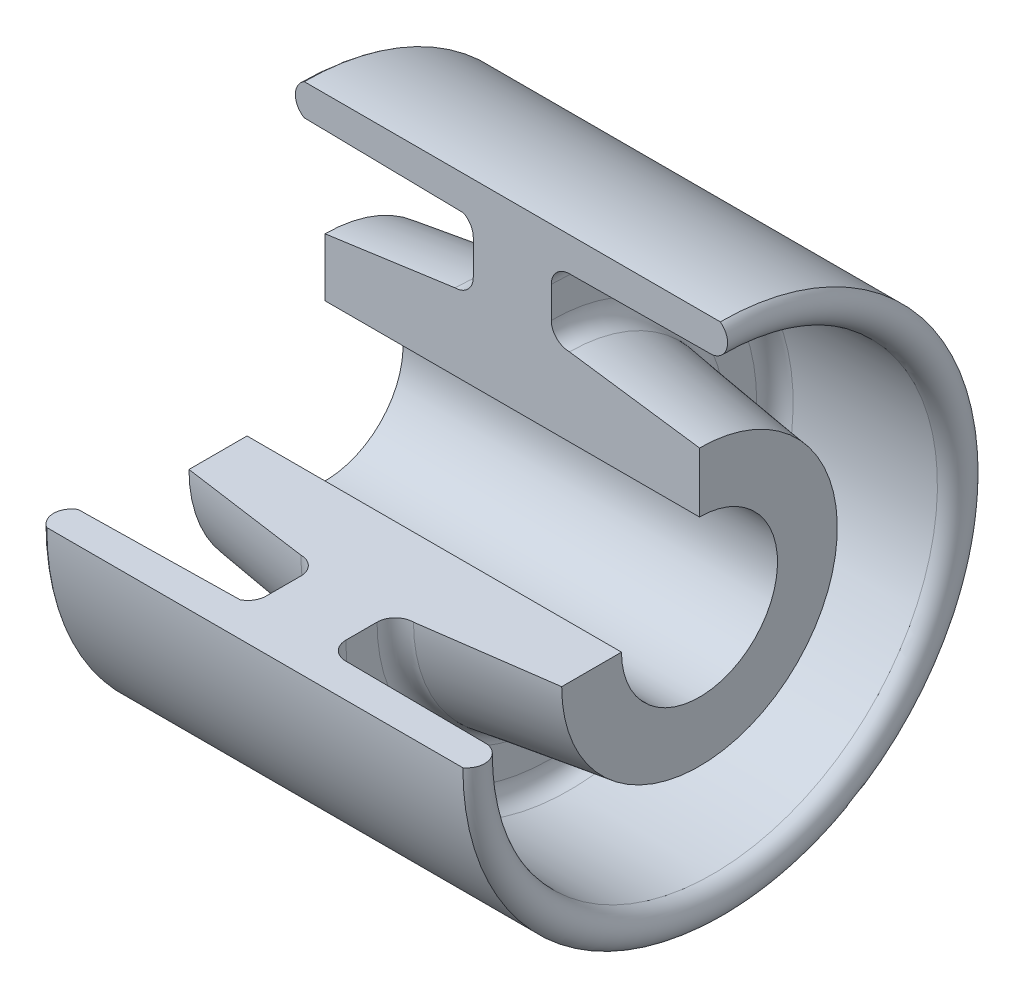
SolidWorks part; units mm, degrees
ref_plane "Front Plane" through (0, 0, 0) normal (0, 0, 1) x (1, 0, 0)
ref_plane "Top Plane" through (0, 0, 0) normal (0, 1, 0) x (1, 0, 0)
ref_plane "Right Plane" through (0, 0, 0) normal (1, 0, 0) x (0, 0, -1)
sketch "Sketch1" plane through (0, 0, 0) normal (0, 0, 1) x (1, 0, 0)
  line L0 (-50.6321, 30.5282) -> (29.3679, 30.5282)
  line L1 (25.3679, -3.9718) -> (25.3679, -18.9718) construction
  line L2 (35.3913, -18.9718) -> (-59.7616, -18.9718) construction
  line L4 (-18.1321, 20.8659) -> (-18.1321, 14.1905)
  line L5 (-3.1321, 20.5282) -> (-3.1321, 14.5282)
  line L7 (-46.6321, -3.9718) -> (25.3679, -3.9718)
  line L10 (25.3679, -3.9718) -> (25.3679, 7.5282)
  line L11 (-46.6321, -3.9718) -> (-46.6321, 7.1905)
  line L14 (-50.6321, 24.506) -> (-20.0232, 23.9742)
  line L15 (27.8679, 24.2766) -> (0.3679, 24.0282)
  line L16 (-46.6321, 7.1905) -> (-21.6321, 10.6905)
  line L18 (25.3679, 7.5282) -> (0.3679, 11.0282)
  arc A0 (27.8679, 24.2766) -> (29.3679, 30.5282) centre (27.2716, 27.7254) ccw
  arc A1 (-50.6321, 30.5282) -> (-50.6321, 24.506) centre (-48.848, 27.5171) ccw
  arc A2 (0.3679, 24.0282) -> (-3.1321, 20.5282) centre (0.3679, 20.5282) ccw
  arc A4 (-3.1321, 14.5282) -> (0.3679, 11.0282) centre (0.3679, 14.5282) ccw
  arc A5 (-21.6321, 10.6905) -> (-18.1321, 14.1905) centre (-21.6321, 14.1905) ccw
  arc A7 (-18.1321, 20.8659) -> (-20.0232, 23.9742) centre (-21.6321, 20.8659) ccw
  point P27 (-10.6321, -3.9718)
  point P35 (-21.6321, 14.1905)
revolve "Revolve2" add sketch "Sketch1" angle 270 about L2
